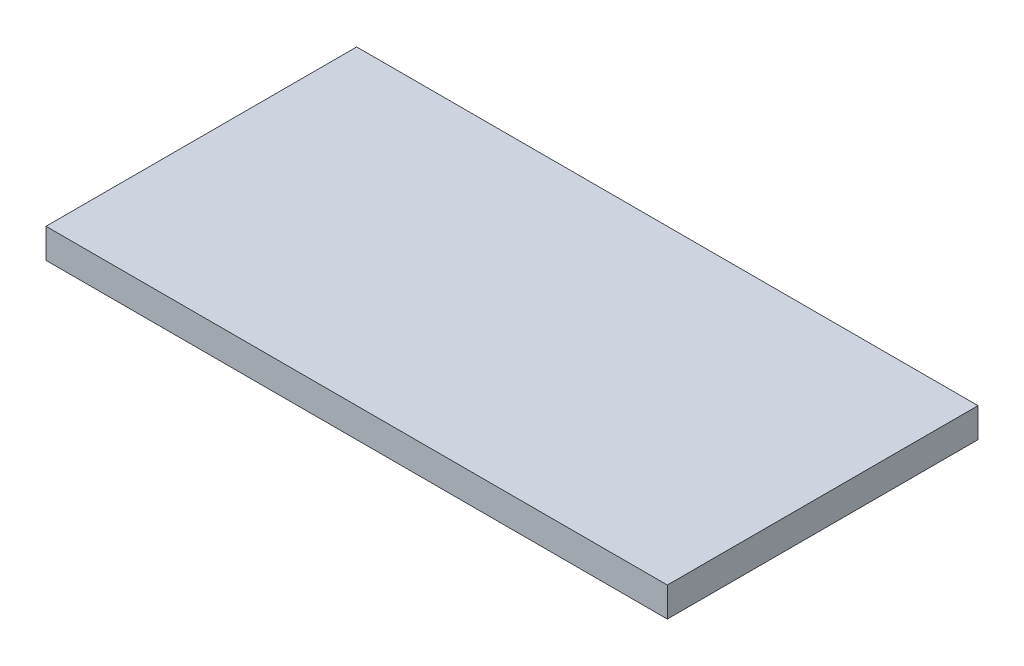
SolidWorks part; units mm, degrees
ref_plane "Front Plane" through (0, 0, 0) normal (0, 0, 1) x (1, 0, 0)
ref_plane "Top Plane" through (0, 0, 0) normal (0, 1, 0) x (1, 0, 0)
ref_plane "Right Plane" through (0, 0, 0) normal (1, 0, 0) x (0, 0, -1)
sketch "Sketch1" plane through (0, 0, 0) normal (0, 1, 0) x (1, 0, 0)
  line L1 (-200, -100) -> (200, -100)
  line L2 (-200, -100) -> (-200, 100)
  line L3 (-200, 100) -> (200, 100)
  line L4 (200, -100) -> (200, 100)
  line L5 (-200, -100) -> (200, 100) construction
  line L6 (-200, 100) -> (200, -100) construction
  point P0 (0, 0)
  dimension "D1" = 200
  dimension "D2" = 400
extrude "Boss-Extrude1" add sketch "Sketch1" against normal blind 19
